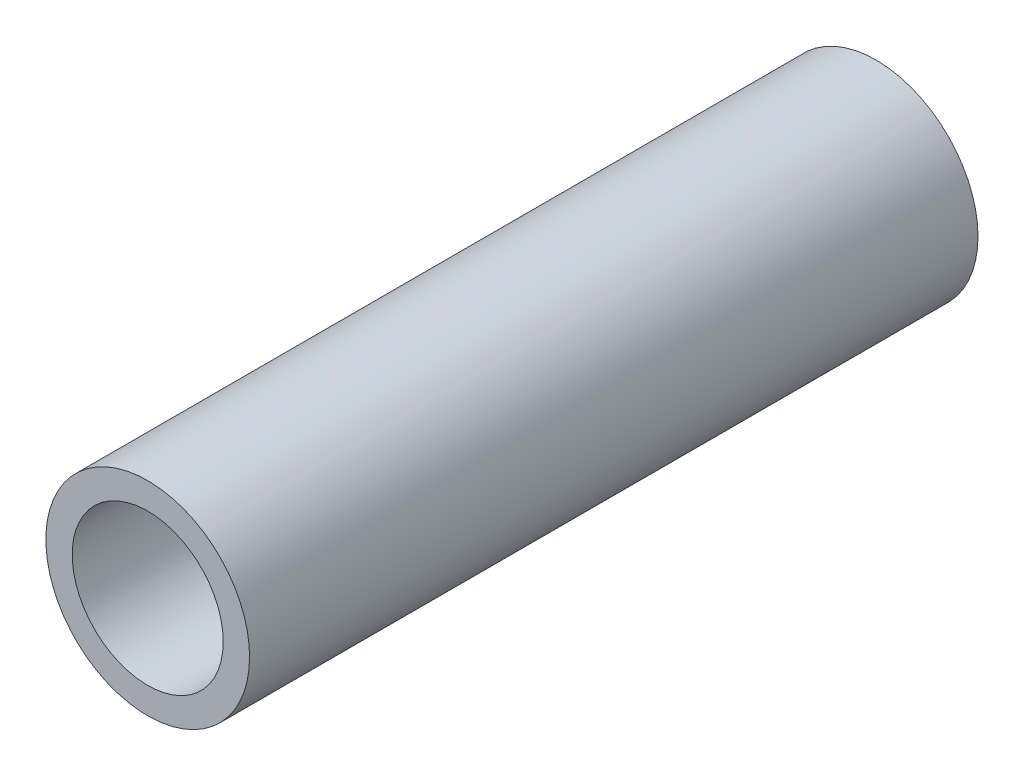
SolidWorks part; units mm, degrees
material "PVC Rigid"
ref_plane "Front Plane" through (0, 0, 0) normal (0, 0, 1) x (1, 0, 0)
ref_plane "Top Plane" through (0, 0, 0) normal (0, 1, 0) x (1, 0, 0)
ref_plane "Right Plane" through (0, 0, 0) normal (1, 0, 0) x (0, 0, -1)
sketch "Sketch1" plane through (0, 0, 0) normal (0, 0, 1) x (1, 0, 0)
  circle A0 centre (0, 0) radius 10.6553
  circle A2 centre (0, 0) radius 7.8994
  dimension "D1" = 21.3106
  dimension "D2" = 15.7988
extrude "Boss-Extrude1" add sketch "Sketch1" along normal blind 76.2
